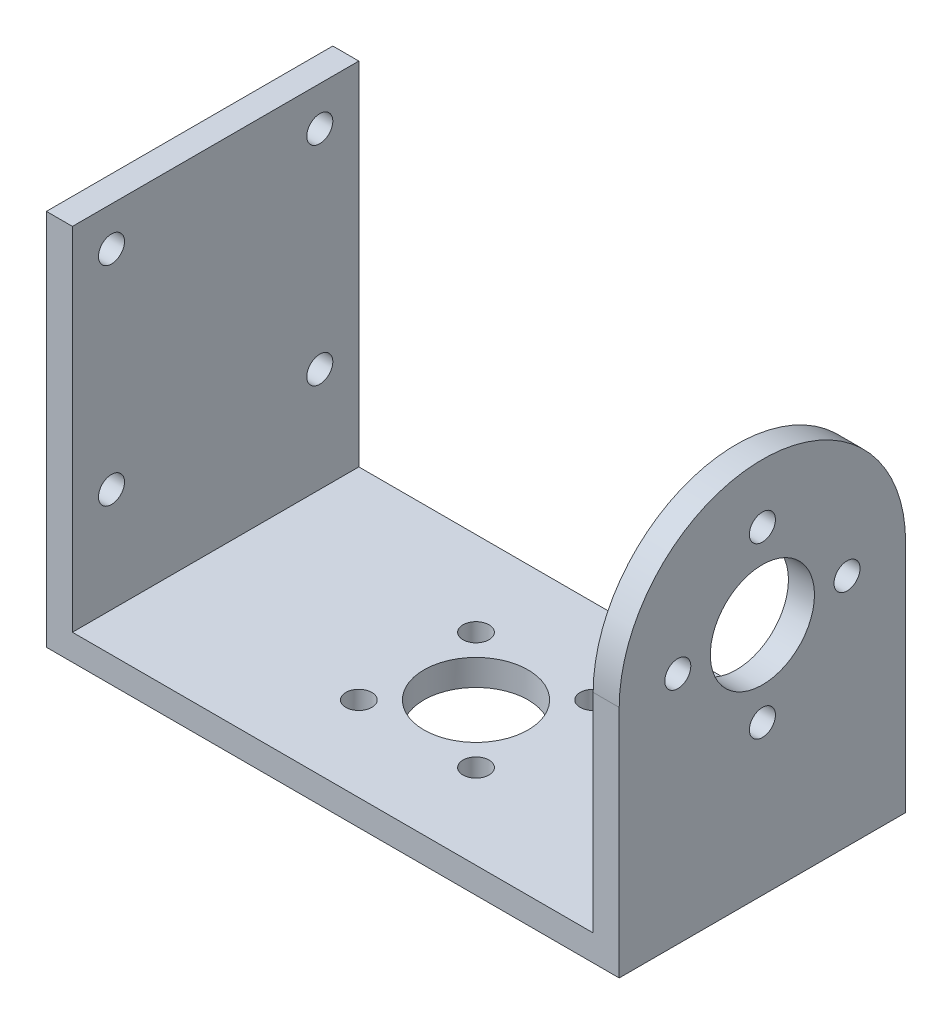
SolidWorks part; units mm, degrees
ref_plane "Front Plane" through (0, 0, 0) normal (0, 0, 1) x (1, 0, 0)
ref_plane "Top Plane" through (0, 0, 0) normal (0, 1, 0) x (1, 0, 0)
ref_plane "Right Plane" through (0, 0, 0) normal (1, 0, 0) x (0, 0, -1)
sketch "Sketch1" plane through (0, 0, 0) normal (0, 1, 0) x (1, 0, 0)
  line L1 (0, 0) -> (44, 0)
  line L2 (0, 0) -> (0, 22)
  line L3 (0, 22) -> (44, 22)
  line L4 (44, 0) -> (44, 22)
  dimension "D1" = 44
  dimension "D2" = 22
extrude "Boss-Extrude1" add sketch "Sketch1" along normal blind 2
sketch "Sketch2" plane through (0, 2, 0) normal (0, 1, 0) x (1, 0, 0)
  line L0 (0, 0) -> (44, 0) construction
  line L1 (0, 22) -> (2, 22)
  line L2 (0, 22) -> (0, 0)
  line L3 (0, 0) -> (2, 0)
  line L4 (2, 22) -> (2, 0)
  line L6 (44, 22) -> (42, 22)
  line L7 (44, 22) -> (44, 0)
  line L8 (44, 0) -> (42, 0)
  line L9 (42, 22) -> (42, 0)
  dimension "D1" = 2
  dimension "D2" = 2
extrude "Boss-Extrude2" add sketch "Sketch2" along normal blind 27
sketch "Sketch3" plane through (44, 0, 0) normal (1, 0, 0) x (0, 0, -1)
  line L0 (0, 29) -> (0, 0) construction
  line L1 (22, 29) -> (22, 0) construction
  line L2 (0, 29) -> (22, 29) construction
  line L3 (22, 18) -> (0, 18) construction
  line L7 (0, 29) -> (0, 18)
  line L8 (11, 29) -> (22, 29)
  line L9 (22, 29) -> (22, 18)
  line L10 (11.2261, 29) -> (0, 29)
  line L11 (0, 29) -> (0, 18)
  arc A0 (0, 18) -> (22, 18) centre (11, 18) cw
  dimension "D1" = 11
  dimension "D2" = 11
extrude "Cut-Extrude1" cut sketch "Sketch3" against normal up to next
sketch "Sketch4" plane through (0, 0, 0) normal (-1, 0, 0) x (0, 0, 1)
  line L0 (0, 29) -> (0, 0) construction
  line L5 (-22, 29) -> (0, 29) construction
  line L6 (-22, 29) -> (-22, 7) construction
  line L7 (-22, 7) -> (0, 7) construction
  line L8 (0, 29) -> (0, 7) construction
  line L9 (-19, 10) -> (-3, 10) construction
  line L10 (-3, 26) -> (-3, 10) construction
  line L11 (-19, 26) -> (-3, 26) construction
  line L12 (-19, 26) -> (-19, 10) construction
  circle A0 centre (-19, 10) radius 1
  circle A1 centre (-19, 26) radius 1
  circle A2 centre (-3, 10) radius 1
  circle A3 centre (-3, 26) radius 1
  dimension "D2" = 2
  dimension "D3" = 2
  dimension "D4" = 2
  dimension "D5" = 2
  dimension "D1" = 22
extrude "Cut-Extrude2" cut sketch "Sketch4" against normal up to next
sketch "Sketch5" plane through (44, 0, 0) normal (1, 0, 0) x (0, 0, -1)
  line L0 (22, 18) -> (0, 18) construction
  line L1 (11, 29) -> (11, 9.1735) construction
  arc A0 (22, 18) -> (0, 18) centre (11, 18) ccw construction
  circle A1 centre (11, 18) radius 6.5 construction
  circle A2 centre (11, 18) radius 4
  circle A3 centre (17.5, 18) radius 1
  circle A4 centre (11, 24.5) radius 1
  circle A5 centre (4.5, 18) radius 1
  circle A6 centre (11, 11.5) radius 1
  dimension "D1" = 13
  dimension "D2" = 8
  dimension "D3" = 2
  dimension "D4" = 2
  dimension "D5" = 2
  dimension "D6" = 2
extrude "Cut-Extrude3" cut sketch "Sketch5" against normal up to next
sketch "Sketch6" plane through (0, 2, 0) normal (0, 1, 0) x (1, 0, 0)
  line L0 (42, 0) -> (2, 22) construction
  line L1 (17.5, 6.5) -> (26.5, 15.5) construction
  line L2 (26.5, 6.5) -> (17.5, 6.5)
  line L3 (26.5, 6.5) -> (26.5, 15.5)
  line L4 (26.5, 15.5) -> (17.5, 15.5)
  line L5 (17.5, 6.5) -> (17.5, 15.5)
  circle A0 centre (22, 11) radius 4
  circle A1 centre (26.5, 6.5) radius 1
  circle A2 centre (17.5, 6.5) radius 1
  circle A3 centre (17.5, 15.5) radius 1
  circle A4 centre (26.5, 15.5) radius 1
  point P12 (22, 11)
  dimension "D1" = 8
  dimension "D4" = 2
  dimension "D5" = 2
  dimension "D6" = 2
  dimension "D7" = 2
  dimension "D2" = 9
  dimension "D3" = 9
extrude "Cut-Extrude4" cut sketch "Sketch6" against normal up to surface (5 mm away) contours L2 A1 L3 | L3 A1 L2 | A2 | A3 | A4 | A0
